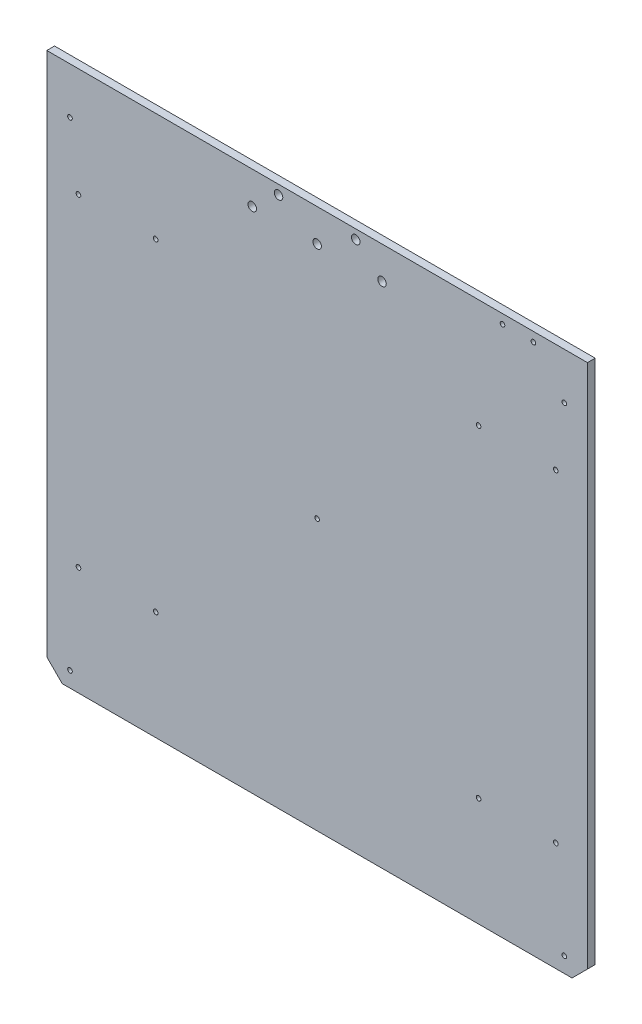
SolidWorks part; units mm, degrees
material "Lega 1060"
ref_plane "Piano frontale" through (0, 0, 0) normal (0, 0, 1) x (1, 0, 0)
ref_plane "Piano superiore" through (0, 0, 0) normal (0, 1, 0) x (1, 0, 0)
ref_plane "Piano destro" through (0, 0, 0) normal (1, 0, 0) x (0, 0, -1)
sketch "Schizzo13" plane through (0, 0, 0) normal (0, 0, 1) x (1, 0, 0)
  line L0 (175, 350) -> (175, 0) construction
  line L1 (10, 0) -> (340, 0)
  line L2 (0, 10) -> (0, 350)
  line L3 (0, 350) -> (350, 350)
  line L4 (350, 10) -> (350, 350)
  line L5 (350, 175) -> (0, 175) construction
  line L6 (-60.1887, 10) -> (461.2643, 10) construction
  line L7 (279.5, 279.5) -> (279.5, 175) construction
  line L8 (-12.961, 344) -> (386.8832, 344) construction
  line L9 (-12.961, 329) -> (386.8832, 329) construction
  line L10 (279.5, 70.5) -> (279.5, 175) construction
  line L11 (279.5, 70.5) -> (175, 70.5) construction
  line L12 (70.5, 70.5) -> (175, 70.5) construction
  line L13 (70.5, 70.5) -> (70.5, 175) construction
  line L14 (70.5, 279.5) -> (70.5, 175) construction
  line L15 (70.5, 279.5) -> (175, 279.5) construction
  line L16 (175, 279.5) -> (329.5, 279.5) construction
  line L17 (329.5, 70.5) -> (329.5, 279.5) construction
  line L18 (20.5, 70.5) -> (329.5, 70.5) construction
  line L19 (20.5, 70.5) -> (20.5, 279.5) construction
  line L20 (175, 279.5) -> (20.5, 279.5) construction
  line L21 (15, -40.9714) -> (15, 408.5301) construction
  line L22 (335, -40.9714) -> (335, 408.5301) construction
  line L23 (-12.961, 320) -> (386.8832, 320) construction
  line L24 (10, 0) -> (0, 10)
  line L25 (340, 0) -> (350, 10)
  circle A0 centre (15, 320) radius 1.5
  circle A1 centre (20.5, 279.5) radius 1.5
  circle A2 centre (70.5, 279.5) radius 1.5
  circle A3 centre (175, 175) radius 1.5
  circle A5 centre (20.5, 70.5) radius 1.5
  circle A6 centre (200, 344) radius 2.75
  circle A7 centre (150, 344) radius 2.75
  circle A8 centre (175, 329) radius 2.75
  circle A9 centre (217, 329) radius 2.75
  circle A10 centre (133, 329) radius 2.75
  circle A11 centre (70.5, 70.5) radius 1.5
  circle A12 centre (279.5, 70.5) radius 1.5
  circle A13 centre (329.5, 70.5) radius 1.5
  circle A14 centre (335, 10) radius 1.5
  circle A15 centre (15, 10) radius 1.5
  circle A16 centre (279.5, 279.5) radius 1.5
  circle A17 centre (329.5, 279.5) radius 1.5
  circle A18 centre (335, 320) radius 1.5
  circle A19 centre (295, 344) radius 1.5
  circle A20 centre (315, 344) radius 1.5
  point P0 (0, 0)
  point P3 (350, 0)
  point P7 (175, 175)
  point P25 (175, 344)
  point P30 (175, 329)
  point P41 (175, 175)
  point P43 (329.5, 175)
  point P46 (15, 320)
  point P54 (335, 320)
  point P55 (335, 10)
  point P56 (15, 10)
  point P57 (15, 320)
  point P58 (335, 320)
  point P59 (15, 10)
  point P60 (335, 10)
  dimension "D5" = 42
  dimension "D6" = 5.5
  dimension "D7" = 25
  dimension "D8" = 15
  dimension "D10" = 154.5
  dimension "D3" = 104.5
  dimension "D17" = 20
  dimension "D1" = 350
  dimension "D2" = 350
  dimension "D4" = 104.5
  dimension "D9" = 6
  dimension "D11" = 104.5
  dimension "D12" = 10
  dimension "D13" = 15
  dimension "D14" = 30
  dimension "D15" = 310
  dimension "D16" = 320
  dimension "D18" = 35
extrude "Estrusione-Estrusione2" add sketch "Schizzo13" against normal blind 5
